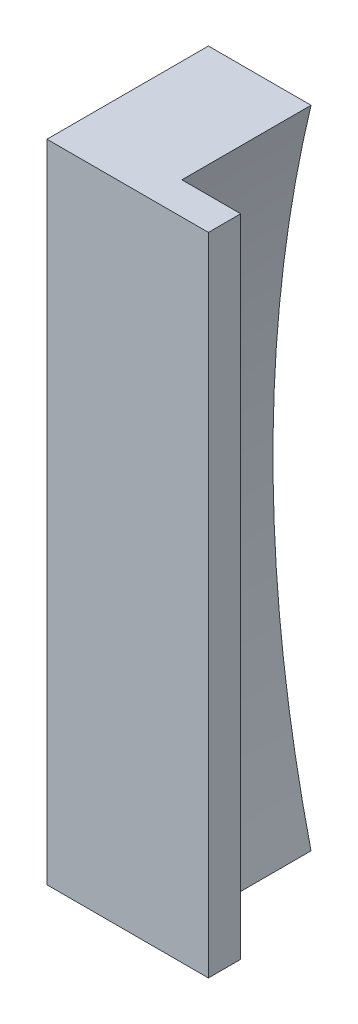
SolidWorks part; units mm, degrees
material "3.1325 (EN-AW 2017A)"
ref_plane "Plan de face" through (0, 0, 0) normal (0, 0, 1) x (1, 0, 0)
ref_plane "Plan de dessus" through (0, 0, 0) normal (0, 1, 0) x (1, 0, 0)
ref_plane "Plan de droite" through (0, 0, 0) normal (1, 0, 0) x (0, 0, -1)
sketch "Esquisse1" plane through (0, 0, 0) normal (0, 0, 1) x (1, 0, 0)
  line L0 (-225, 50) -> (-225, -50)
  line L1 (-225, 50) -> (-209.1052, 50)
  line L2 (-225, -50) -> (-209.1052, -50)
  arc A0 (-209.1052, 50) -> (-209.1052, -50) centre (0, 0) ccw
  dimension "D1" = 50
  dimension "D2" = 100
  dimension "D3" = 225
extrude "Boss.-Extru.1" add sketch "Esquisse1" along normal blind 20
sketch "Esquisse9" plane through (0, 0, 20) normal (0, 0, 1) x (1, 0, 0)
  line L1 (-225, -50) -> (-200, -50)
  line L2 (-225, -50) -> (-225, 50)
  line L3 (-225, 50) -> (-200, 50)
  line L4 (-200, -50) -> (-200, 50)
  dimension "D1" = 25
extrude "Boss.-Extru.2" add sketch "Esquisse9" along normal blind 5
hole_wizard "Chambrage pour vis à tête hexagonale M53" positions "Esquisse11" profile "Esquisse10" counterbore size "M5" standard "ISO" end condition through all
sketch "Esquisse11" plane through (-225, 0, 0) normal (-1, 0, 0) x (0, 0, 1)
  line L0 (0, 50) -> (0, -50) construction
  point P0 (16, 35)
  point P2 (0, 0)
  dimension "D1" = 35
  dimension "D2" = 16
sketch "Esquisse10" plane through (-225, 35, 16) normal (0, 1, 0) x (0, 0, 1)
  line L0 (0, 0) -> (0, 25)
  line L1 (0, 25) -> (2.75, 25)
  line L3 (2.75, 25) -> (2.75, 5)
  line L4 (2.75, 5) -> (5, 5)
  line L5 (5, 5) -> (5, 0)
  line L7 (5, 0) -> (0, 0)
  line L11 (0, -6.35) -> (0, 107.95) construction
  dimension "Diamètre du perçage jusqu'au prochain" = 5.5
  dimension "Profondeur du perçage jusqu'au prochain" = 25
  dimension "Diamètre du chambrage" = 10
  dimension "Profondeur du chambrage" = 5
hole_wizard "Chambrage pour vis à tête hexagonale M54" positions "Esquisse13" profile "Esquisse12" counterbore size "M5" standard "ISO" end condition through all
sketch "Esquisse13" plane through (-225, 0, 0) normal (-1, 0, 0) x (0, 0, 1)
  line L0 (0, 50) -> (0, -50) construction
  line L1 (25, -50) -> (0, -50) construction
  point P0 (16, -35)
  dimension "D1" = 16
  dimension "D2" = 15
sketch "Esquisse12" plane through (-225, -35, 16) normal (0, 1, 0) x (0, 0, 1)
  line L0 (0, 0) -> (0, 25)
  line L1 (0, 25) -> (2.75, 25)
  line L3 (2.75, 25) -> (2.75, 5)
  line L4 (2.75, 5) -> (5, 5)
  line L5 (5, 5) -> (5, 0)
  line L7 (5, 0) -> (0, 0)
  line L11 (0, -6.35) -> (0, 107.95) construction
  dimension "Diamètre du perçage jusqu'au prochain" = 5.5
  dimension "Profondeur du perçage jusqu'au prochain" = 25
  dimension "Diamètre du chambrage" = 10
  dimension "Profondeur du chambrage" = 5
hole_wizard "Trou taraudé M52" positions "Esquisse17" profile "Esquisse16" tap size "M5" standard "ISO" end condition through all
sketch "Esquisse17" plane through (-225, 0, 0) normal (-1, 0, 0) x (0, 0, 1)
  line L0 (0, 50) -> (0, -50) construction
  line L1 (20, 0) -> (0, 0) construction
  point P0 (12.5, 20)
  point P6 (12.5, -20)
  dimension "D1" = 12.5
  dimension "D2" = 20
  dimension "D3" = 20
  dimension "D4" = 12.5
sketch "Esquisse16" plane through (-225, 20, 12.5) normal (0, 1, 0) x (0, 0, 1)
  line L0 (0, 0) -> (0, 25)
  line L1 (0, 25) -> (2.1, 25)
  line L2 (2.1, 25) -> (2.1, 0)
  line L5 (2.1, 0) -> (0, 0)
  line L11 (0, -6.35) -> (0, 107.95) construction
  dimension "Diamètre du trou pour taraudage jusqu'au prochain" = 4.2
  dimension "Profondeur du trou pour taraudage jusqu'au prochain" = 25
cosmetic thread "Filetage de perçage4" parameters "D2"=5
cosmetic thread "Filetage de perçage5" parameters "D2"=5
